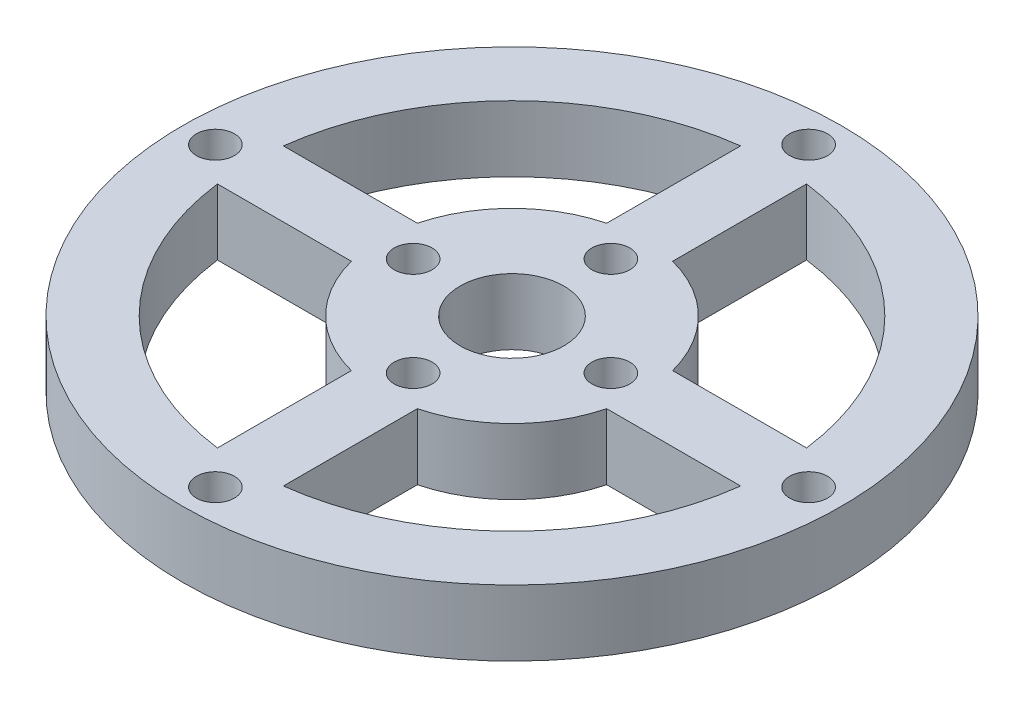
SolidWorks part; units mm, degrees
material "AISI 316 Stainless Steel Sheet (SS)"
ref_plane "Front Plane" through (0, 0, 0) normal (0, 0, 1) x (1, 0, 0)
ref_plane "Top Plane" through (0, 0, 0) normal (0, 1, 0) x (1, 0, 0)
ref_plane "Right Plane" through (0, 0, 0) normal (1, 0, 0) x (0, 0, -1)
sketch "Sketch1" plane through (0, 0, 0) normal (0, 1, 0) x (1, 0, 0)
  line L0 (-3.175, 12.2967) -> (-3.175, 25.2008)
  line L1 (3.175, 12.2967) -> (3.175, 25.2008)
  line L2 (-25.2008, 3.175) -> (-12.2967, 3.175)
  line L3 (-25.2008, -3.175) -> (-12.2967, -3.175)
  line L4 (-3.175, -25.2008) -> (-3.175, -12.2967)
  line L5 (3.175, -25.2008) -> (3.175, -12.2967)
  line L6 (25.2008, 3.175) -> (12.2967, 3.175)
  line L7 (25.2008, -3.175) -> (12.2967, -3.175)
  circle A0 centre (0, 0) radius 5
  circle A1 centre (0, 0) radius 12.7
  circle A2 centre (0, 0) radius 25.4
  circle A3 centre (0, 0) radius 31.75
  point P22 (0, 0)
  dimension "D1" = 10
  dimension "D2" = 25.4
  dimension "D3" = 50.8
  dimension "D4" = 63.5
  dimension "D5" = 6.35
extrude "Boss-Extrude1" add sketch "Sketch1" along normal blind 6.35 contours A3 A2 | A1 A0 | L2 A2 L3 A1 | L1 A2 L0 A1 | L7 A2 L6 A1 | L4 A2 L5 A1
hole_wizard "#6 Clearance Hole1" positions "3DSketch1" profile "Sketch2" hole size "#6" standard "ANSI Inch"
sketch3d "3DSketch1"
  line L0 (0, 0, 0) -> (0, 6.35, 0) construction
  line L1 (0, 6.35, 0) -> (0, 6.35, 9.525) construction
  line L2 (0, 6.35, 31.75) -> (0, 6.35, 28.575) construction
  circle A0 centre (0, 6.35, 0) radius 31.75 construction
  point P6 (0, 6.35, 9.525)
  point P16 (0, 38.1, 0)
  point P21 (0, 6.35, 28.575)
  dimension "D1" = 9.525
  dimension "D2" = 3.175
sketch "Sketch2" plane through (0, 6.35, 28.575) normal (1, 0, 0) x (0, 0, 1)
  line L0 (0, 0) -> (0, 13.7989)
  line L1 (0, 13.7989) -> (1.8288, 12.7)
  line L2 (1.8288, 12.7) -> (1.8288, 0)
  line L5 (1.8288, 0) -> (0, 0)
  line L10 (0, 13.7989) -> (-1.8288, 12.7) construction
  line L11 (0, -6.35) -> (0, 107.95) construction
  dimension "Hole Dia." = 3.6576
  dimension "Hole Depth" = 12.7
  dimension "Drill Angle" = 118
pattern_circular "CirPattern1" count 4 over 360 about axis through (0, 0, 0) along (0, 1, 0) of "#6 Clearance Hole1"
